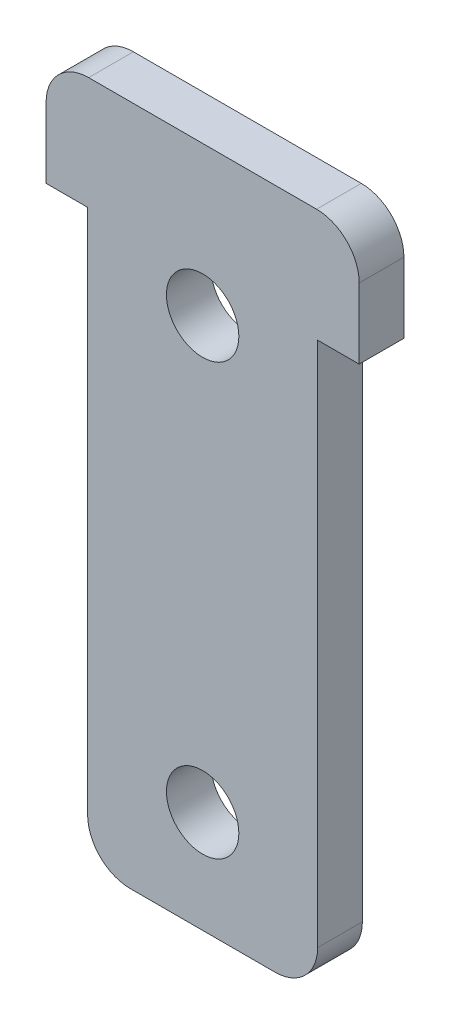
SolidWorks part; units mm, degrees
ref_plane "Front Plane" through (0, 0, 0) normal (0, 0, 1) x (1, 0, 0)
ref_plane "Top Plane" through (0, 0, 0) normal (0, 1, 0) x (1, 0, 0)
ref_plane "Right Plane" through (0, 0, 0) normal (1, 0, 0) x (0, 0, -1)
sketch "Sketch1" plane through (0, 0, 0) normal (0, 0, 1) x (1, 0, 0)
  line L1 (2, 0) -> (8.8, 0)
  line L2 (0, 2) -> (0, 26.7)
  line L3 (0, 26.7) -> (10.8, 26.7)
  line L4 (10.8, 2) -> (10.8, 26.7)
  line L5 (-1.95, 26.7) -> (12.75, 26.7)
  line L6 (-1.95, 26.7) -> (-1.95, 30)
  line L7 (0.05, 32) -> (10.75, 32)
  line L8 (12.75, 26.7) -> (12.75, 30)
  circle A0 centre (5.4, 4.8) radius 1.7
  circle A1 centre (5.4, 25) radius 1.7
  arc A2 (8.8, 0) -> (10.8, 2) centre (8.8, 2) ccw
  arc A3 (2, 0) -> (0, 2) centre (2, 2) cw
  arc A4 (10.75, 32) -> (12.75, 30) centre (10.75, 30) cw
  arc A5 (-1.95, 30) -> (0.05, 32) centre (0.05, 30) cw
  point P9 (5.4, 26.7)
  point P10 (5.4, 26.7)
  point P15 (0, 0)
  point P16 (5.4, 0)
  point P19 (10.8, 0)
  point P22 (0, 0)
  point P25 (12.75, 32)
  point P28 (-1.95, 32)
  dimension "D5" = 3.4
  dimension "D6" = 4.8
  dimension "D7" = 7
  dimension "D8" = 2
  dimension "D1" = 10.8
  dimension "D2" = 14.7
  dimension "D3" = 5.3
  dimension "D4" = 32
extrude "Boss-Extrude1" add sketch "Sketch1" along normal blind 2.1 contours A3 L1 A2 L4 L5 A1 L3 L2 A0 | A5 L6 L5 L3 L8 A4 L7
